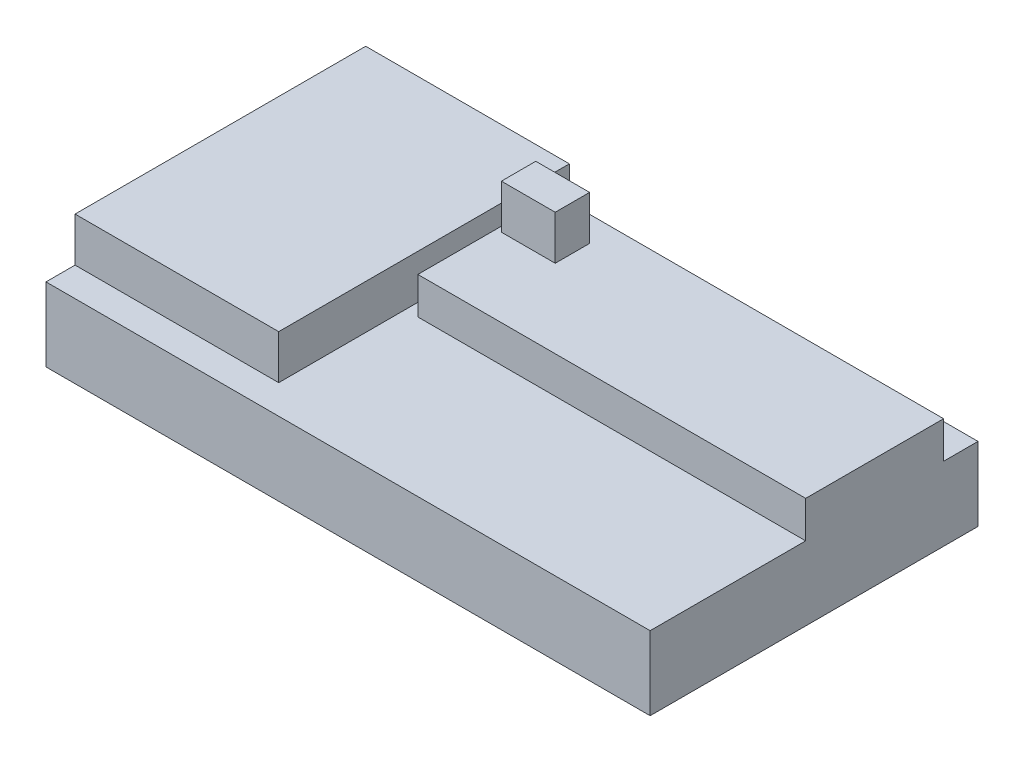
SolidWorks part; units mm, degrees
ref_plane "Front Plane" through (0, 0, 0) normal (0, 0, 1) x (1, 0, 0)
ref_plane "Top Plane" through (0, 0, 0) normal (0, 1, 0) x (1, 0, 0)
ref_plane "Right Plane" through (0, 0, 0) normal (1, 0, 0) x (0, 0, -1)
sketch "Sketch1" plane through (0, 0, 0) normal (0, 1, 0) x (1, 0, 0)
  line L1 (-39.0441, 22.591) -> (42.9559, 22.591)
  line L2 (-39.0441, 22.591) -> (-39.0441, -21.909)
  line L3 (-39.0441, -21.909) -> (42.9559, -21.909)
  line L4 (42.9559, 22.591) -> (42.9559, -21.909)
  dimension "D1" = 44.5
  dimension "D2" = 82
extrude "Boss-Extrude1" add sketch "Sketch1" along normal blind 10
sketch "Sketch2" plane through (0, 10, 0) normal (0, 1, 0) x (1, 0, 0)
  line L0 (42.9559, -21.909) -> (42.9559, 22.591) construction
  line L1 (42.9559, 17.9246) -> (-9.6821, 17.9246)
  line L2 (42.9559, 17.9246) -> (42.9559, -0.7975)
  line L3 (42.9559, -0.7975) -> (-9.6821, -0.7975)
  line L4 (-9.6821, 17.9246) -> (-9.6821, -0.7975)
extrude "Boss-Extrude2" add sketch "Sketch2" along normal blind 5
sketch "Sketch3" plane through (0, 10, 0) normal (0, 1, 0) x (1, 0, 0)
  line L0 (-39.0441, 22.591) -> (-39.0441, -21.909) construction
  line L1 (-39.0441, 21.4845) -> (-11.4023, 21.4845)
  line L2 (-39.0441, 21.4845) -> (-39.0441, -17.9657)
  line L3 (-39.0441, -17.9657) -> (-11.4023, -17.9657)
  line L4 (-11.4023, 21.4845) -> (-11.4023, -17.9657)
extrude "Boss-Extrude3" add sketch "Sketch3" along normal blind 6
sketch "Sketch4" plane through (0, 15, 0) normal (0, 1, 0) x (1, 0, 0)
  line L1 (-8.9803, 14.5036) -> (-1.6726, 14.5036)
  line L2 (-8.9803, 14.5036) -> (-8.9803, 9.8359)
  line L3 (-8.9803, 9.8359) -> (-1.6726, 9.8359)
  line L4 (-1.6726, 14.5036) -> (-1.6726, 9.8359)
extrude "Boss-Extrude4" add sketch "Sketch4" along normal blind 6
